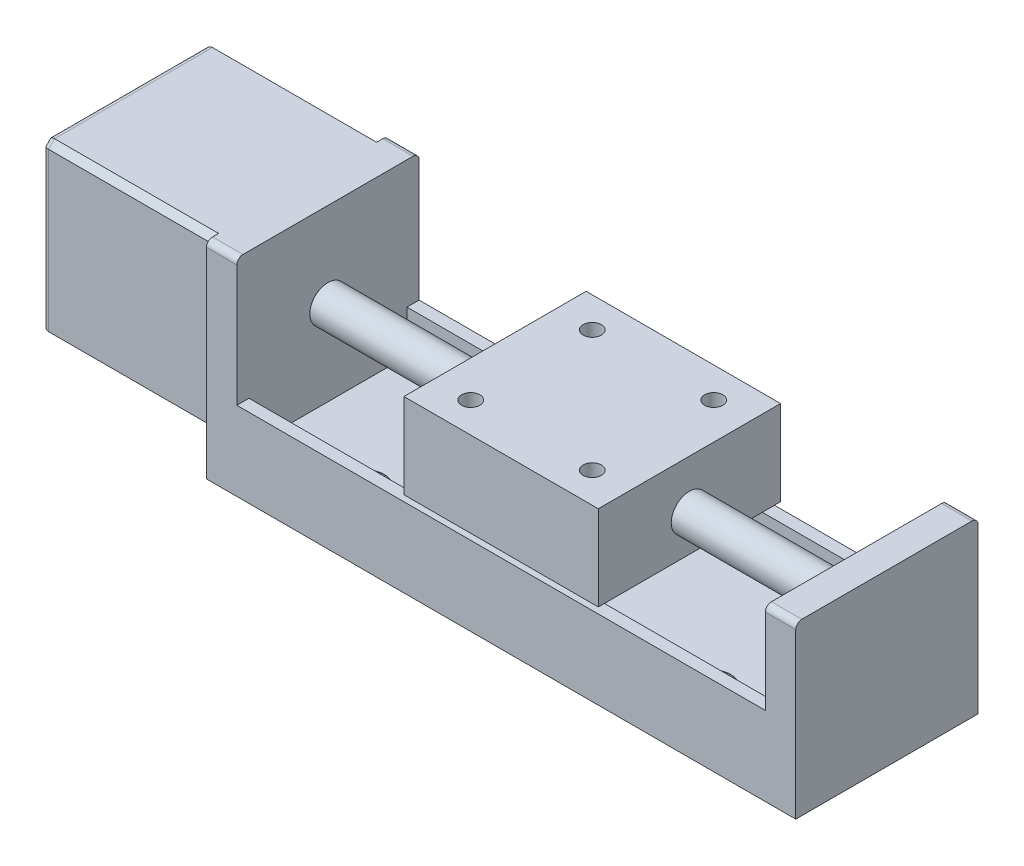
SolidWorks part; units mm, degrees
material "1060 Alloy"
ref_plane "Front Plane" through (0, 0, 0) normal (0, 0, 1) x (1, 0, 0)
ref_plane "Top Plane" through (0, 0, 0) normal (0, 1, 0) x (1, 0, 0)
ref_plane "Right Plane" through (0, 0, 0) normal (1, 0, 0) x (0, 0, -1)
sketch "Sketch1" plane through (0, 0, 0) normal (0, 0, 1) x (1, 0, 0)
  line L0 (-78.5, 34) -> (-78.5, 6)
  line L1 (-78.5, 6) -> (-48.5, 6)
  line L2 (-48.5, 6) -> (-48.5, 0)
  line L3 (-48.5, 0) -> (48.5, 0)
  line L4 (48.5, 0) -> (48.5, 28)
  line L5 (48.5, 28) -> (43.5, 28)
  line L6 (43.5, 28) -> (43.5, 13)
  line L7 (43.5, 13) -> (-43.5, 13)
  line L8 (-43.5, 13) -> (-43.5, 34)
  line L11 (-43.5, 34) -> (-78.5, 34)
  point P11 (0, 0)
  dimension "D1" = 5
  dimension "D2" = 5
  dimension "D3" = 13
  dimension "D4" = 28
  dimension "D5" = 30
  dimension "D6" = 28
  dimension "D7" = 34
  dimension "D8" = 127
extrude "Boss-Extrude1" add sketch "Sketch1" along normal mid plane 30
sketch "Sketch2" plane through (0, 13, 0) normal (0, 1, 0) x (1, 0, 0)
  line L0 (-43.5, -15) -> (-43.5, 15) construction
  line L1 (-43.5, -13) -> (43.5, -13)
  line L2 (-43.5, -13) -> (-43.5, 13)
  line L3 (-43.5, 13) -> (43.5, 13)
  line L4 (43.5, -13) -> (43.5, 13)
  line L5 (-43.5, -13) -> (43.5, 13) construction
  line L6 (-43.5, 13) -> (43.5, -13) construction
  line L7 (43.5, -15) -> (-43.5, -15) construction
  point P0 (0, 0)
  dimension "D1" = 2
extrude "Cut-Extrude1" cut sketch "Sketch2" against normal offset from surface (7 mm away) 6 up to face at (0, 0, 0)
sketch "Sketch3" plane through (48.5, 0, 0) normal (1, 0, 0) x (0, 0, -1)
  circle A0 centre (0, 20) radius 3
  dimension "D1" = 20
  dimension "D2" = 6
extrude "Boss-Extrude2" add sketch "Sketch3" against normal up to surface (92 mm away) up to face at (-43.5, 16.5, 0)
sketch "Sketch4" plane through (0, 34, 0) normal (0, 1, 0) x (1, 0, 0)
  line L0 (-48.5, 14) -> (-48.5, -14) construction
  line L3 (-48.5, -14) -> (-76.5, -14)
  line L4 (-76.5, -14) -> (-76.5, 14)
  line L5 (-76.5, 14) -> (-48.5, 14)
  line L6 (-43.5, -13) -> (-43.5, 13) construction
  line L7 (-43.5, 0) -> (-48.5, 0) construction
  line L8 (-43.5, -15) -> (-43.5, 15) construction
  line L9 (-48.5, -14) -> (-48.5, -15)
  line L10 (-43.5, -15) -> (-78.5, -15) construction
  line L11 (-48.5, -15) -> (-78.5, -15)
  line L12 (-78.5, -15) -> (-78.5, 15)
  line L13 (-78.5, 15) -> (-48.5, 15)
  line L14 (-43.5, 15) -> (-78.5, 15) construction
  line L15 (-48.5, 15) -> (-48.5, 14)
  line M7 (-43.5, 15) -> (-78.5, 15)
  line M8 (-78.5, 15) -> (-78.5, -15)
  line M9 (-78.5, -15) -> (-43.5, -15)
  dimension "D1" = 5
  dimension "D2" = 28
  dimension "D3" = 28
extrude "Cut-Extrude2" cut sketch "Sketch4" against normal through all contours L15 L9 L3 L4 L5 M7 M8 M9
chamfer "Chamfer1" distance 1 angle 45 4 edges at (-62.5, 6, 14) (-62.5, 6, -14) (-62.5, 34, -14) (-62.5, 34, 14)
fillet "Fillet1" radius 1 8 edges at (-76.5, 6.5, -13.5) (-76.5, 20, -14) (-76.5, 33.5, -13.5) (-76.5, 34, 0) (-76.5, 33.5, 13.5) (-76.5, 20, 14) (-76.5, 6.5, 13.5) (-76.5, 6, 0)
fillet "Fillet2" radius 1 4 edges at (46, 28, 15) (46, 28, -15) (-46, 34, -15) (-46, 34, 15)
hole_wizard "CBORE for M3 Hex Socket Head Cap Screw1" positions "Sketch5" profile "Sketch6" counterbore size "M3" standard "ISO" end condition through all
sketch "Sketch5" plane through (0, 6, 0) normal (0, 1, 0) x (1, 0, 0)
  line L0 (-28.5, 8.0068) -> (28.5, 8.0068) construction
  line L1 (28.5, 8.0068) -> (28.5, -8.9932) construction
  line L2 (28.5, -8.9932) -> (-28.5, -8.9932) construction
  line L3 (-28.5, -8.9932) -> (-28.5, 8.0068) construction
  line L5 (43.5, -14) -> (43.5, 14) construction
  line L6 (-43.5, -13) -> (-43.5, 13) construction
  point P0 (-28.5, 8.0068)
  point P2 (-28.5, -8.9932)
  point P4 (28.5, 8.0068)
  point P6 (28.5, -8.9932)
  dimension "D1" = 17
  dimension "D2" = 15
  dimension "D3" = 15
sketch "Sketch6" plane through (-28.5, 6, -8.0068) normal (1, 0, 0) x (0, 0, 1)
  line L0 (0, 0) -> (0, 6)
  line L1 (0, 6) -> (1.7, 6)
  line L3 (1.7, 6) -> (1.7, 3.4)
  line L4 (3.25, 3.4) -> (1.7, 3.4)
  line L5 (3.25, 3.4) -> (3.25, 0.025)
  line L6 (3.25, 0.025) -> (3.275, 0)
  line L7 (3.275, 0) -> (0, 0)
  line L8 (-3.25, 0.025) -> (-3.275, 0) construction
  line L11 (0, -6.35) -> (0, 107.95) construction
  dimension "Thru Hole Dia." = 3.4
  dimension "Thru Hole Depth" = 6
  dimension "C'Bore Dia." = 6.5
  dimension "C'Bore Depth" = 3.4
  dimension "Near C'Sink Dia." = 6.55
  dimension "Near C'Sink Angle" = 90
sketch "Sketch7" plane through (0, 28, 0) normal (0, 1, 0) x (1, 0, 0)
  line L1 (-16, -15) -> (16, -15)
  line L2 (-16, -15) -> (-16, 15)
  line L3 (-16, 15) -> (16, 15)
  line L4 (16, -15) -> (16, 15)
  line L5 (-16, -15) -> (16, 15) construction
  line L6 (-16, 15) -> (16, -15) construction
  point P0 (0, 0)
  dimension "D1" = 30
  dimension "D2" = 32
extrude "Boss-Extrude3" add sketch "Sketch7" against normal offset from surface (14 mm away) 1 up to face at (0, 13, 14)
sketch "Sketch8" plane through (0, 28, 0) normal (0, 1, 0) x (1, 0, 0)
  line L0 (-10, 10) -> (10, 10) construction
  line L1 (10, 10) -> (10, -10) construction
  line L2 (10, -10) -> (-10, -10) construction
  line L3 (-10, -10) -> (-10, 10) construction
  line L4 (16, 15) -> (-16, 15) construction
  line L5 (-16, 15) -> (-16, -15) construction
  circle A0 centre (-10, 10) radius 1.5 construction
  circle A1 centre (10, 10) radius 1.5 construction
  circle A2 centre (10, -10) radius 1.5 construction
  circle A3 centre (-10, -10) radius 1.5 construction
  dimension "D1" = 3
  dimension "D2" = 17
  dimension "D3" = 17
  dimension "D4" = 3.5
  dimension "D5" = 4.5
hole_wizard "Hole1" positions "Sketch9" profile "Sketch10" legacy
sketch "Sketch9" plane through (0, 28, 0) normal (0, 1, 0) x (1, 0, 0)
  point P0 (10, 10)
  point P3 (10, -10)
  point P6 (-10, -10)
  point P9 (-10, 10)
sketch "Sketch10" plane through (10, 28, -10) normal (1, 0, 0) x (0, 0, 1)
  line L0 (0, 0) -> (0, 6)
  line L1 (0, 6) -> (1.5, 6)
  line L2 (1.5, 6) -> (1.5, 0)
  line L3 (1.5, 0) -> (0, 0)
  line L4 (0, 110) -> (0, -10) construction
  dimension "Diameter" = 3
  dimension "Depth" = 6
